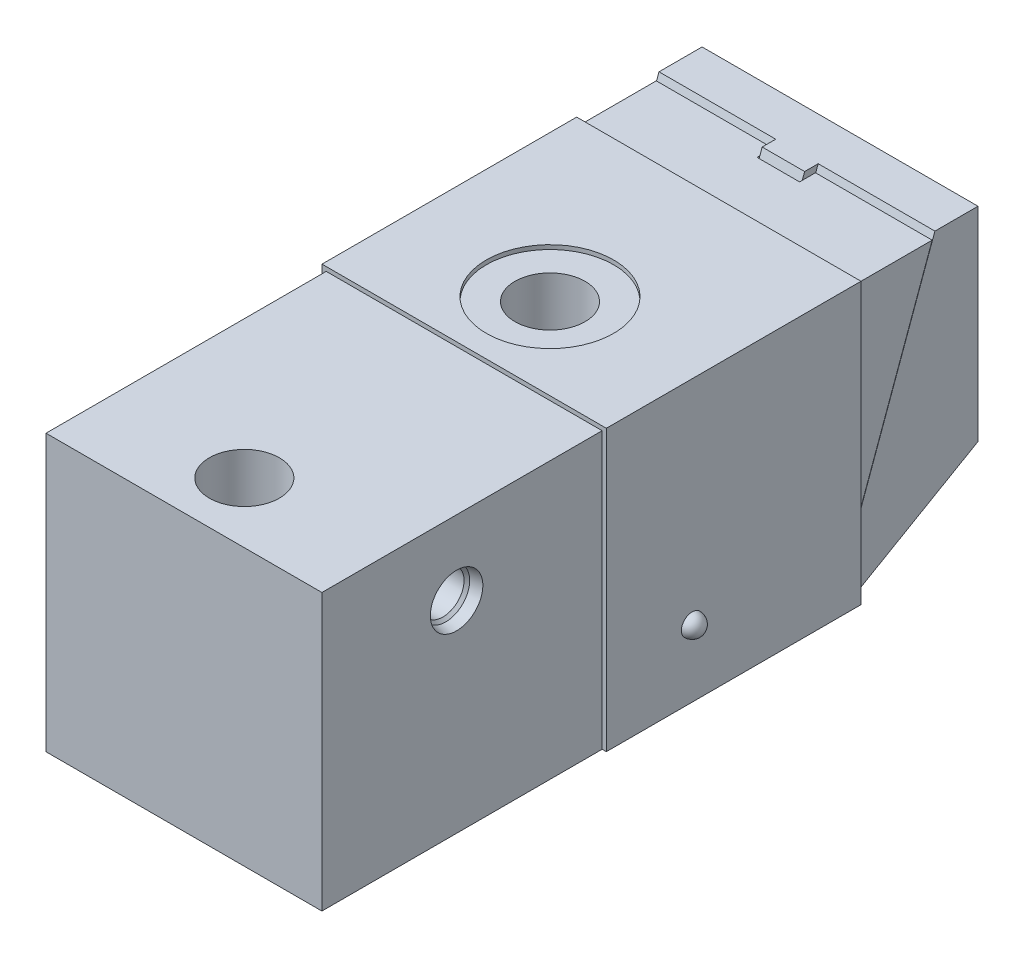
SolidWorks part; units mm, degrees
material "Alloy Steel"
ref_plane "Front Plane" through (0, 0, 0) normal (0, 0, 1) x (1, 0, 0)
ref_plane "Top Plane" through (0, 0, 0) normal (0, 1, 0) x (1, 0, 0)
ref_plane "Right Plane" through (0, 0, 0) normal (1, 0, 0) x (0, 0, -1)
sketch "Sketch1" plane through (0, 0, 0) normal (1, 0, 0) x (0, 0, -1)
  line L0 (0, 0) -> (107.0102, 0)
  line L1 (107.0102, 0) -> (107.0102, 64.9986)
  line L2 (107.0102, 64.9986) -> (0, 64.9986)
  line L3 (0, 64.9986) -> (0, 0)
  dimension "D1" = 64.9986
  dimension "D2" = 107.0102
extrude "Extrude1" add sketch "Sketch1" along normal mid plane 64.9986
sketch "Sketch11" plane through (0, 0, 0) normal (1, 0, 0) x (0, 0, -1)
  line L0 (144.4097, 66.5226) -> (154.559, 66.5226)
  line L1 (154.559, 66.5226) -> (154.559, 18.5166)
  line L2 (154.559, 18.5166) -> (125.127, 1.524)
  line L3 (125.127, 1.524) -> (120.7521, 1.524)
  line L4 (120.7521, 1.524) -> (144.4097, 66.5226)
  line L5 (0, 64.9986) -> (0, 0) construction
  line L6 (0, 0) -> (107.0102, 0) construction
  dimension "D1" = 30
  dimension "D2" = 16.9926
  dimension "D3" = 10.1493
  dimension "D4" = 20
  dimension "D5" = 154.559
  dimension "D6" = 1.524
  dimension "D7" = 64.9986
extrude "Extrude4" add sketch "Sketch11" along normal mid plane 65.0001 separate body
sketch "Sketch12" plane through (0, 0, 0) normal (1, 0, 0) x (0, 0, -1)
  line L0 (144.4097, 66.5226) -> (120.7521, 1.524)
  line L1 (120.7521, 1.524) -> (117.5596, 1.524)
  line L2 (117.5596, 1.524) -> (141.2171, 66.5226)
  line L3 (141.2171, 66.5226) -> (144.4097, 66.5226)
  line L4 (154.559, 66.5226) -> (144.4097, 66.5226) construction
  dimension "D1" = 3
extrude "Extrude5" add sketch "Sketch12" along normal mid plane 10
sketch "Sketch13" plane through (0, 0, 0) normal (1, 0, 0) x (0, 0, -1)
  line L0 (76.8573, 31.0241) -> (105.1345, 31.0241) construction
  line L1 (154.559, 36.5241) -> (147.259, 36.5241)
  line L2 (154.559, 18.5166) -> (154.559, 66.5226) construction
  line L3 (147.259, 36.5241) -> (147.259, 34.124)
  line L4 (147.259, 34.124) -> (142.6591, 34.124)
  line L5 (142.6591, 34.124) -> (142.6591, 44.024)
  line L6 (142.6591, 44.024) -> (110.9091, 44.024)
  line L7 (110.9091, 44.024) -> (110.9091, 31.0241)
  line L8 (110.9091, 31.0241) -> (154.559, 31.0241)
  line L9 (154.559, 31.0241) -> (154.559, 36.5241)
  line L10 (120.7521, 1.524) -> (125.127, 1.524) construction
  dimension "D1" = 29.5001
  dimension "D2" = 25.9999
  dimension "D3" = 31.75
  dimension "D4" = 11
  dimension "D5" = 7.3
  dimension "D6" = 11.8999
  dimension "D7" = 6.1999
revolve "Cut-Revolve4" cut sketch "Sketch13" angle 360 about L0
sketch "Sketch14" plane through (0, 0, -147.259) normal (0, 0, -1) x (-1, 0, 0)
  circle A0 centre (0, 31.0241) radius 5.0038
  dimension "D1" = 10.0076
extrude "Extrude6" add sketch "Sketch14" along normal blind 5.9944
sketch "Sketch15" plane through (0, 0, -153.2534) normal (0, 0, -1) x (-1, 0, 0)
  line L1 (3.4609, 31.0241) -> (1.7304, 34.0213)
  line L2 (1.7304, 34.0213) -> (-1.7304, 34.0213)
  line L3 (-1.7304, 34.0213) -> (-3.4609, 31.0241)
  line L4 (-3.4609, 31.0241) -> (-1.7304, 28.0269)
  line L5 (-1.7304, 28.0269) -> (1.7304, 28.0269)
  line L6 (1.7304, 28.0269) -> (3.4609, 31.0241)
  circle A0 centre (0, 31.0241) radius 2.9972 construction
  dimension "D1" = 5.9944
extrude "Cut-Extrude3" cut sketch "Sketch15" against normal up to surface (5.9944 mm away) up to face at (5.5, 31.0241, -147.259)
sketch "Sketch2" plane through (0, 0, 0) normal (1, 0, 0) x (0, 0, -1)
  line L0 (113.2593, 64.9986) -> (113.2593, 2.0066)
  line L1 (113.2593, 2.0066) -> (120.8375, 2.0066)
  line L2 (120.8375, 2.0066) -> (143.7647, 64.9986)
  line L3 (143.7647, 64.9986) -> (113.2593, 64.9986)
  line L4 (107.0102, 64.9986) -> (0, 64.9986) construction
  line L5 (144.4097, 66.5226) -> (120.7521, 1.524) construction
  dimension "D1" = 62.992
  dimension "D2" = 30.5054
  dimension "D3" = 0.0848
extrude "Extrude2" add sketch "Sketch2" against normal mid plane 64.9986 separate body
sketch "Sketch3" plane through (0, 0, 0) normal (1, 0, 0) x (0, 0, -1)
  line L0 (140.0309, 64.9986) -> (117.1037, 2.0066)
  line L1 (140.0309, 64.9986) -> (143.7647, 64.9986)
  line L2 (143.7647, 64.9986) -> (120.8375, 2.0066)
  line L3 (120.8375, 2.0066) -> (117.1037, 2.0066)
  line L4 (143.7647, 64.9986) -> (113.2593, 64.9986) construction
  line L5 (113.2593, 2.0066) -> (120.8375, 2.0066) construction
  line L6 (120.8375, 2.0066) -> (143.7647, 64.9986) construction
  dimension "D1" = 3.7338
extrude "Cut-Extrude1" cut sketch "Sketch3" against normal mid plane 10.0076
sketch "Sketch4" plane through (0, 0, 0) normal (0, -1, 0) x (1, 0, 0)
  line L0 (32.4993, 0) -> (-32.4993, 0) construction
  circle A0 centre (0, -14.224) radius 8.255
  circle A1 centre (0, -86.233) radius 8.255
  dimension "D1" = 16.51
  dimension "D2" = 72.009
  dimension "D3" = 14.224
extrude "Cut-Extrude2" cut sketch "Sketch4" against normal up to next (64.9986 mm away)
hole_wizard "Hole1" positions "Sketch17" profile "Sketch16" legacy
sketch "Sketch17" plane through (0, 0, 0) normal (0, -1, 0) x (1, 0, 0)
  line L0 (0, 0) -> (0, -63.3687) construction
  line L1 (32.4993, 0) -> (-32.4993, 0) construction
  point P0 (-23.495, -14.224)
  point P8 (-23.495, -97.2312)
  point P12 (23.495, -14.224)
  point P13 (23.495, -97.2312)
  dimension "D1" = 23.495
  dimension "D2" = 14.224
  dimension "D3" = 83.0072
sketch "Sketch16" plane through (-23.495, 0, -14.224) normal (1, 0, 0) x (0, 0, -1)
  line L0 (0, 0) -> (0, 19.0086)
  line L1 (0, 19.0086) -> (5.0038, 16.002)
  line L2 (5.0038, 16.002) -> (5.0038, 0)
  line L4 (5.0038, 0) -> (0, 0)
  line L6 (0, 19.0086) -> (-5.0038, 16.002) construction
  line L7 (0, -4.2442) -> (0, 117.3081) construction
  dimension "Diameter" = 10.0076
  dimension "Depth" = 16.002
  dimension "Drill Angle" = 118
ref_plane "Plane14" through (0, 47.498, 0) normal (0, -1, 0) x (1, 0, 0)
sketch "S2D0001" plane through (14.986, 47.498, -21.336) normal (0, -1, 0) x (0, 0, -1)
  line L0 (10.3886, 17.5133) -> (16.5735, 17.5133)
  line L1 (16.5735, 17.5133) -> (16.0309, 14.9606)
  line L2 (16.0309, 14.9606) -> (15.367, 14.2967)
  line L3 (15.367, 14.2967) -> (15.367, -20.5867)
  line L4 (15.367, -20.5867) -> (10.3886, -20.5867)
  line L5 (10.3886, -20.5867) -> (10.3886, 17.5133)
  line L6 (10.3886, -25.3864) -> (10.3886, 0.762) construction
  line L7 (-21.336, 17.5133) -> (85.6742, 17.5133) construction
  circle A0 centre (-7.112, -14.986) radius 8.255 construction
  dimension "D2" = 17.5006
  dimension "D1" = 38.1
  dimension "D3" = 9.9568
  dimension "D4" = 12.3698
  dimension "D5" = 2.5527
  dimension "D6" = 12
  dimension "D7" = 45
revolve "Cut-Revolve2" cut sketch "S2D0001" angle 360 about L6
mirror "Mirror1" about plane through (0, 0, 0) normal (1, 0, 0) of "Cut-Revolve2"
sketch "Sketch19" plane through (0, 0, 0) normal (1, 0, 0) x (0, 0, -1)
  line L0 (31.7246, 47.498) -> (31.7246, -8.8821) construction
  line L1 (36.0426, 0) -> (36.0426, 1.5875)
  line L2 (0, 0) -> (107.0102, 0) construction
  line L3 (36.0426, 1.5875) -> (34.2265, 1.5875)
  line L4 (34.2265, 1.5875) -> (34.2265, 47.498)
  line L5 (34.2265, 47.498) -> (31.7246, 47.498)
  line L6 (31.7246, 47.498) -> (31.7246, 0)
  line L7 (31.7246, 0) -> (36.0426, 0)
  dimension "D1" = 1.5875
  dimension "D2" = 5.0038
  dimension "D3" = 8.636
revolve "Cut-Revolve5" cut sketch "Sketch19" angle 360 about L0
sketch "Sketch8" plane through (0, 0, 0) normal (1, 0, 0) x (0, 0, -1)
  line L0 (31.7246, -0.5194) -> (31.7246, 1.6878) construction
  line L1 (0, 0) -> (107.0102, 0) construction
  line L2 (29.2227, 43.1939) -> (29.2227, 1.5875) construction
  line L3 (34.2265, 1.5875) -> (34.2265, 43.1939) construction
  circle A0 centre (35.0393, 0.5842) radius 1.0033
  dimension "D1" = 2.0066
  dimension "D2" = 6.6294
  dimension "D3" = 0.5842
revolve "Revolve1" add sketch "Sketch8" angle 360 about L0
ref_plane "Plane15" through (0, 0, -126.0094) normal (0, 0, -1) x (-1, 0, 0)
sketch "Sketch9" plane through (0, 0, -126.0094) normal (0, 0, -1) x (-1, 0, 0)
  line L0 (32.4993, 64.9986) -> (32.4993, 0)
  line L1 (32.4993, 64.9986) -> (-32.4993, 64.9986)
  line L2 (-32.4993, 64.9986) -> (-32.4993, 0)
  line L3 (-32.4993, 0) -> (-33.4899, 0)
  line L4 (-33.4899, 0) -> (-33.4899, 65.9892)
  line L5 (-33.4899, 65.9892) -> (33.4899, 65.9892)
  line L6 (33.4899, 65.9892) -> (33.4899, 0)
  line L7 (33.4899, 0) -> (32.4993, 0)
  line L8 (32.4993, 64.9986) -> (32.4993, 0) construction
  line L9 (-32.4993, 64.9986) -> (32.4993, 64.9986) construction
  line L10 (-32.4993, 64.9986) -> (-32.4993, 0) construction
  line L11 (-32.4993, 0) -> (32.4993, 0) construction
  dimension "D1" = 0.9906
  dimension "D2" = 0.9906
extrude "Extrude3" add sketch "Sketch9" against normal blind 59.9948 separate body
ref_plane "Plane16" through (0, 15.875, 0) normal (0, -1, 0) x (1, 0, 0)
sketch "Sketch10" plane through (0, 15.875, -83.7438) normal (0, 1, 0) x (1, 0, 0)
  line L0 (33.4899, 5.0292) -> (33.4899, 2.4892)
  line L1 (-33.4899, 5.0292) -> (-33.4899, 2.4892)
  line L2 (33.4899, 2.4892) -> (36.0299, 2.4892)
  line L3 (-36.0299, 2.4892) -> (-33.4899, 2.4892)
  line L4 (-20.3683, 2.4892) -> (20.3683, 2.4892) construction
  line L5 (-33.4899, -17.7292) -> (-33.4899, 42.2656) construction
  line L6 (33.4899, -17.7292) -> (33.4899, 42.2656) construction
  arc A0 (36.0299, 2.4892) -> (33.4899, 5.0292) centre (33.4899, 2.4892) ccw
  arc A1 (-33.4899, 5.0292) -> (-36.0299, 2.4892) centre (-33.4899, 2.4892) ccw
  dimension "D2" = 2.54
  dimension "D1" = 72.009
revolve "Revolve2" add sketch "Sketch10" angle 360 about L4
sketch "Sketch18" plane through (0, 65.9892, 0) normal (0, 1, 0) x (1, 0, 0)
  circle A0 centre (0, 86.233) radius 14.9987
  dimension "D1" = 29.9974
extrude "Cut-Extrude4" cut sketch "Sketch18" against normal up to surface (0.9906 mm away) up to face at (0, 64.9986, -94.488)
sketch "Sketch20" plane through (0, 0, 0) normal (0, -1, 0) x (1, 0, 0)
  circle A0 centre (0, -86.233) radius 16.002
  dimension "D1" = 32.004
extrude "Cut-Extrude5" cut sketch "Sketch20" against normal blind 5.842
